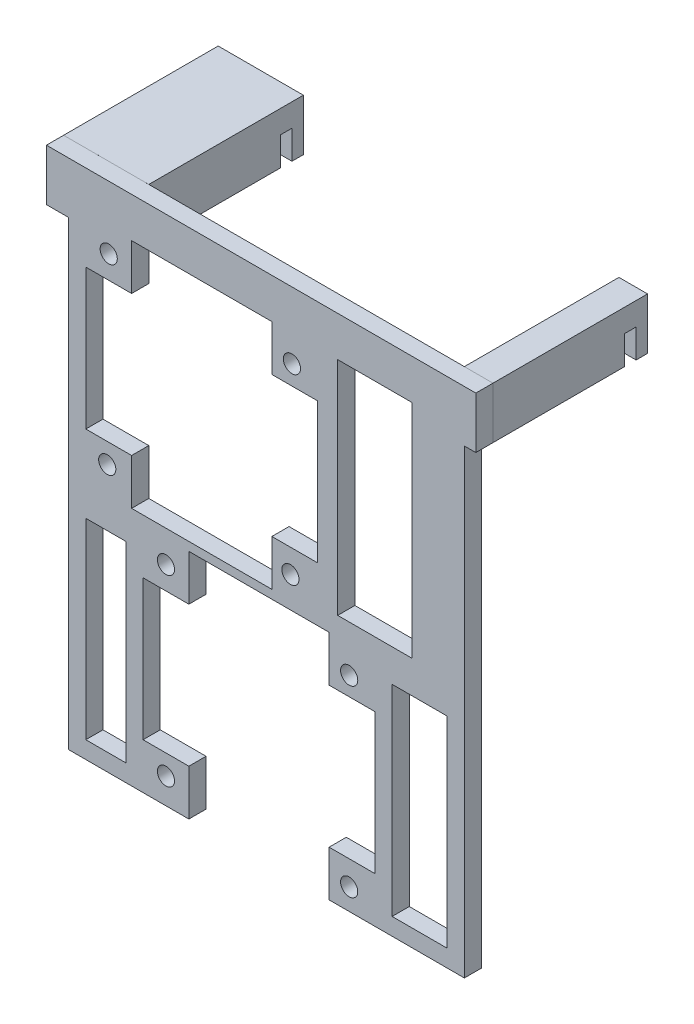
SolidWorks part; units mm, degrees
ref_plane "Alzado" through (0, 0, 0) normal (0, 0, 1) x (1, 0, 0)
ref_plane "Planta" through (0, 0, 0) normal (0, 1, 0) x (1, 0, 0)
ref_plane "Vista lateral" through (0, 0, 0) normal (1, 0, 0) x (0, 0, -1)
sketch "Croquis1" plane through (0, 0, 0) normal (0, 0, 1) x (1, 0, 0)
  line L0 (24.5732, 17.7353) -> (29.5732, 17.7353)
  line L1 (-45.4268, 17.7353) -> (-30.5468, 17.7353)
  line L4 (-45.4268, 17.7353) -> (-45.4268, 8.7353)
  line L5 (24.5732, 17.7353) -> (24.5732, 8.7353)
  line L7 (-45.4268, 8.7353) -> (-30.5468, 8.7353)
  line L8 (-30.5468, 8.7353) -> (-30.5468, 17.7353)
  line L9 (29.5732, 17.7353) -> (29.5732, 8.7353)
  line L10 (29.5732, 8.7353) -> (24.5732, 8.7353)
  dimension "D6" = 5
  dimension "D1" = 75
  dimension "D2" = 14.88
  dimension "D3" = 9
  dimension "D4" = 9
extrude "Saliente-Extruir1" add sketch "Croquis1" along normal blind 27
sketch "Croquis2" plane through (0, 0, 27) normal (0, 0, 1) x (1, 0, 0)
  line L0 (-45.4259, 8.7343) -> (-41.5487, 8.7343)
  line L1 (29.5741, 8.7343) -> (29.5732, 17.7353)
  line L2 (-41.5487, -71.7657) -> (-28.5487, -71.7657)
  line L3 (-45.4259, 17.7343) -> (-45.4259, 8.7343)
  line L4 (-41.5487, 8.7343) -> (-41.5487, -71.7657)
  line L5 (-28.5487, -71.7657) -> (-20.5487, -71.7657)
  line L6 (-20.5487, -71.7657) -> (-20.5487, -63.7657)
  line L7 (-20.5487, -63.7657) -> (-28.5487, -63.7657)
  line L8 (-28.5487, -63.7657) -> (-28.5487, -39.2657)
  line L9 (-28.5487, -39.2657) -> (-20.5487, -39.2657)
  line L10 (-20.5487, -39.2657) -> (-20.5487, -31.2657)
  line L11 (-20.5487, -31.2657) -> (3.9513, -31.2657)
  line L12 (3.9513, -31.2657) -> (3.9513, -39.2657)
  line L13 (3.9513, -39.2657) -> (11.9513, -39.2657)
  line L14 (11.9513, -39.2657) -> (11.9513, -63.7657)
  line L15 (11.9513, -63.7657) -> (3.9513, -63.7657)
  line L16 (3.9513, -63.7657) -> (3.9513, -71.746)
  line L17 (15.9513, -71.746) -> (27.5741, -71.746)
  line L18 (3.9513, -71.746) -> (15.9513, -71.746)
  line L19 (29.5732, 17.7353) -> (-45.4259, 17.7343)
  line L20 (-30.5487, -29.7657) -> (-30.5487, -21.7657)
  line L21 (-30.5487, -21.7657) -> (-38.5487, -21.7657)
  line L22 (-38.5487, -21.7657) -> (-38.5487, 2.7343)
  line L23 (-38.5487, 2.7343) -> (-30.5487, 2.7343)
  line L24 (-30.5487, 2.7343) -> (-30.5487, 10.7343)
  line L25 (-30.5487, 10.7343) -> (-6.0487, 10.7343)
  line L26 (-6.0487, 10.7343) -> (-6.0487, 2.7343)
  line L27 (-6.0487, 2.7343) -> (1.9513, 2.7343)
  line L28 (1.9513, 2.7343) -> (1.9513, -21.7657)
  line L29 (1.9513, -21.7657) -> (-6.0487, -21.7657)
  line L30 (-6.0487, -21.7657) -> (-6.0487, -29.7657)
  line L31 (-6.0487, -29.7657) -> (-30.5487, -29.7657)
  line L32 (14.9513, -33.6303) -> (24.5741, -33.6303)
  line L33 (27.5741, -71.746) -> (27.5741, 8.7343)
  line L34 (27.5741, 8.7343) -> (29.5741, 8.7343)
  line L35 (14.9513, -33.6303) -> (14.9513, -68.746)
  line L36 (14.9513, -68.746) -> (24.5741, -68.746)
  line L37 (24.5741, -33.6303) -> (24.5741, -68.746)
  line L38 (-38.5487, -35.2657) -> (-31.5487, -35.2657)
  line L39 (-38.5487, -35.2657) -> (-38.5487, -68.7657)
  line L40 (-38.5487, -68.7657) -> (-31.5487, -68.7657)
  line L41 (-31.5487, -35.2657) -> (-31.5487, -68.7657)
  line L42 (5.4513, -27.9552) -> (5.4513, 10.7343)
  line L43 (5.4513, 10.7343) -> (18.4513, 10.7343)
  line L44 (5.4513, -27.9552) -> (18.4513, -27.9552)
  line L45 (18.4513, 10.7343) -> (18.4513, -27.9552)
  circle A0 centre (-24.5487, -35.2657) radius 1.5
  circle A1 centre (7.4513, -36.0172) radius 1.5
  circle A2 centre (-24.5487, -67.2657) radius 1.5
  circle A3 centre (7.4513, -68.0172) radius 1.5
  circle A4 centre (-34.5487, 6.7343) radius 1.5
  circle A5 centre (-34.8066, -25.2657) radius 1.5
  circle A6 centre (-2.8066, -25.8921) radius 1.5
  circle A7 centre (-2.5487, 6.1079) radius 1.5
  dimension "D1" = 4
  dimension "D2" = 4
  dimension "D3" = 8
  dimension "D4" = 8
  dimension "D5" = 8
  dimension "D6" = 8
  dimension "D7" = 32
  dimension "D8" = 32
  dimension "D9" = 32
  dimension "D10" = 32
  dimension "D11" = 24.5
  dimension "D12" = 24.5
  dimension "D13" = 8
  dimension "D14" = 8
  dimension "D15" = 4
  dimension "D16" = 4
  dimension "D17" = 24.5
  dimension "D18" = 32
  dimension "D19" = 32
  dimension "D20" = 32
  dimension "D21" = 32
  dimension "D22" = 9.001
  dimension "D23" = 2
  dimension "D24" = 24.5
  dimension "D25" = 40.5
  dimension "D26" = 1.5
  dimension "D27" = 8
  dimension "D28" = 8
  dimension "D29" = 8
  dimension "D30" = 3
  dimension "D31" = 3
  dimension "D32" = 3
  dimension "D33" = 3
  dimension "D34" = 80.4803
  dimension "D35" = 69.1227
extrude "Saliente-Extruir2" add sketch "Croquis2" along normal blind 3
sketch "Croquis3" plane through (29.5732, 0, 0) normal (1, 0, 0) x (0, 0, -1)
  line L0 (-27, 8.7353) -> (0, 8.7353) construction
  line L1 (-2, 8.7353) -> (-4, 8.7353)
  line L2 (-2, 8.7353) -> (-2, 13.7353)
  line L3 (-2, 13.7353) -> (-4, 13.7353)
  line L4 (-4, 8.7353) -> (-4, 13.7353)
  line L5 (0, 8.7353) -> (0, 17.7353) construction
  dimension "D1" = 5
  dimension "D2" = 2
  dimension "D3" = 2
extrude "Cortar-Extruir1" cut sketch "Croquis3" against normal up to vertex
